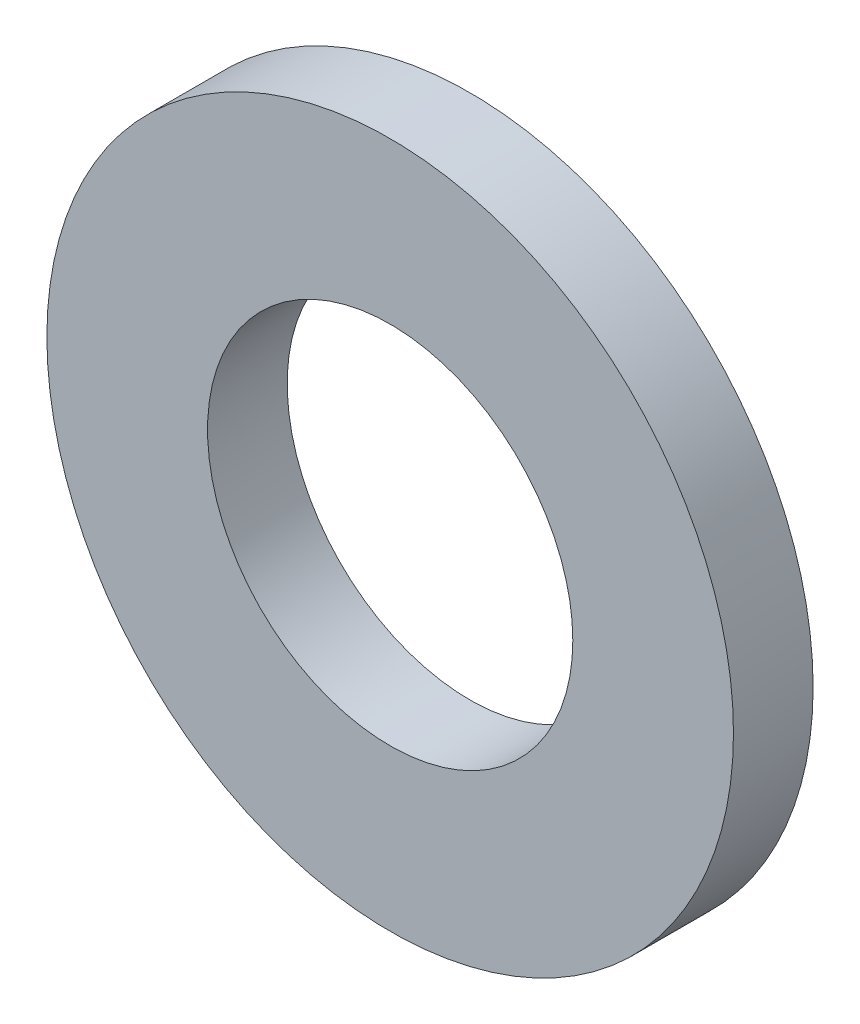
SolidWorks part; units mm, degrees
ref_plane "Front Plane" through (0, 0, 0) normal (0, 0, 1) x (1, 0, 0)
ref_plane "Top Plane" through (0, 0, 0) normal (0, 1, 0) x (1, 0, 0)
ref_plane "Right Plane" through (0, 0, 0) normal (1, 0, 0) x (0, 0, -1)
sketch "Sketch1" plane through (0, 0, 0) normal (0, 0, 1) x (1, 0, 0)
  circle A0 centre (0, 0) radius 6.35
  circle A1 centre (0, 0) radius 3.3782
  dimension "D1" = 12.7
  dimension "D2" = 6.7564
extrude "Boss-Extrude1" add sketch "Sketch1" along normal blind 1.4732
